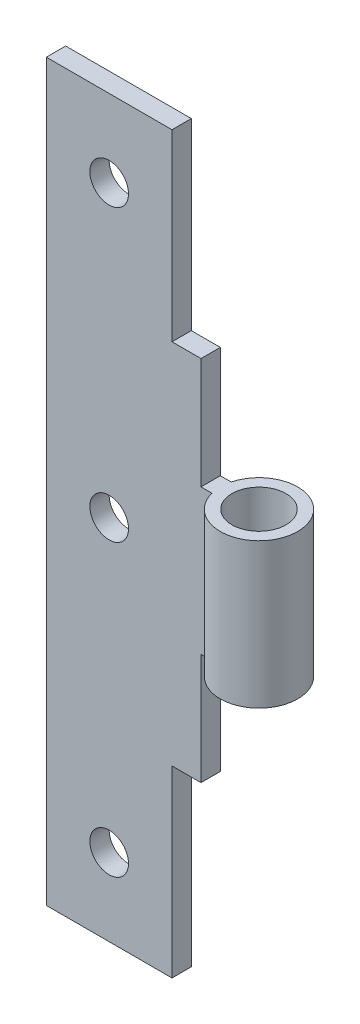
SolidWorks part; units mm, degrees
ref_plane "Front Plane" through (0, 0, 0) normal (0, 0, 1) x (1, 0, 0)
ref_plane "Top Plane" through (0, 0, 0) normal (0, 1, 0) x (1, 0, 0)
ref_plane "Right Plane" through (0, 0, 0) normal (1, 0, 0) x (0, 0, -1)
sketch "Sketch1" plane through (0, 0, 0) normal (0, 1, 0) x (1, 0, 0)
  line L0 (2.3135, 0.5) -> (-6.25, 0.5)
  line L1 (2.3135, -0.5) -> (-6.25, -0.5)
  line L2 (-6.25, 0.5) -> (-6.25, -0.5)
  line L3 (4.25, 0) -> (2.5904, 0) construction
  line L4 (2.25, 0) -> (0.9308, 0) construction
  arc A0 (2.3135, -0.5) -> (2.3135, 0.5) centre (4.25, 0) ccw
  circle A1 centre (4.25, 0) radius 1.4
  dimension "D1" = 4
  dimension "D2" = 2.8
  dimension "D3" = 10.5
  dimension "D4" = 1
extrude "Boss-Extrude1" add sketch "Sketch1" along normal blind 7.5
sketch "Sketch2" plane through (0, 7.5, 0) normal (0, 1, 0) x (1, 0, 0)
  line L0 (-6.25, -0.5) -> (-6.25, 0.5)
  line L1 (-6.25, -0.5) -> (1.75, -0.5)
  line L2 (-6.25, 0.5) -> (1.75, 0.5)
  line L3 (1.75, -0.5) -> (1.75, 0.5)
  dimension "D1" = 8
extrude "Boss-Extrude2" add sketch "Sketch2" along normal blind 5.75
sketch "Sketch3" plane through (0, 0, 0) normal (0, -1, 0) x (1, 0, 0)
  line L0 (-6.25, -0.5) -> (-6.25, 0.5)
  line L1 (-6.25, -0.5) -> (1.75, -0.5)
  line L2 (-6.25, 0.5) -> (1.75, 0.5)
  line L3 (1.75, -0.5) -> (1.75, 0.5)
  dimension "D1" = 8
extrude "Boss-Extrude3" add sketch "Sketch3" along normal blind 5.75
sketch "Sketch4" plane through (0, -5.75, 0) normal (0, -1, 0) x (1, 0, 0)
  line L0 (-6.25, -0.5) -> (-6.25, 0.5)
  line L1 (-6.25, -0.5) -> (0.25, -0.5)
  line L2 (-6.25, 0.5) -> (0.25, 0.5)
  line L3 (0.25, -0.5) -> (0.25, 0.5)
  dimension "D1" = 6.5
extrude "Boss-Extrude4" add sketch "Sketch4" along normal blind 9.5
sketch "Sketch5" plane through (0, 13.25, 0) normal (0, 1, 0) x (1, 0, 0)
  line L0 (-6.25, -0.5) -> (-6.25, 0.5)
  line L1 (-6.25, -0.5) -> (0.25, -0.5)
  line L2 (-6.25, 0.5) -> (0.25, 0.5)
  line L3 (0.25, -0.5) -> (0.25, 0.5)
  dimension "D1" = 6.5
extrude "Boss-Extrude5" add sketch "Sketch5" along normal blind 9.5
sketch "Sketch6" plane through (0, 0, 0.5) normal (0, 0, 1) x (1, 0, 0)
  line L0 (-3, 22.75) -> (-3, -24.0869) construction
  line L1 (-6.25, 22.75) -> (0.25, 22.75) construction
  circle A0 centre (-3, 18.75) radius 1
  circle A1 centre (-3, 3.75) radius 1
  circle A2 centre (-3, -11.25) radius 1
  dimension "D1" = 2
  dimension "D2" = 4
  dimension "D3" = 3
extrude "Cut-Extrude1" cut sketch "Sketch6" against normal up to next
